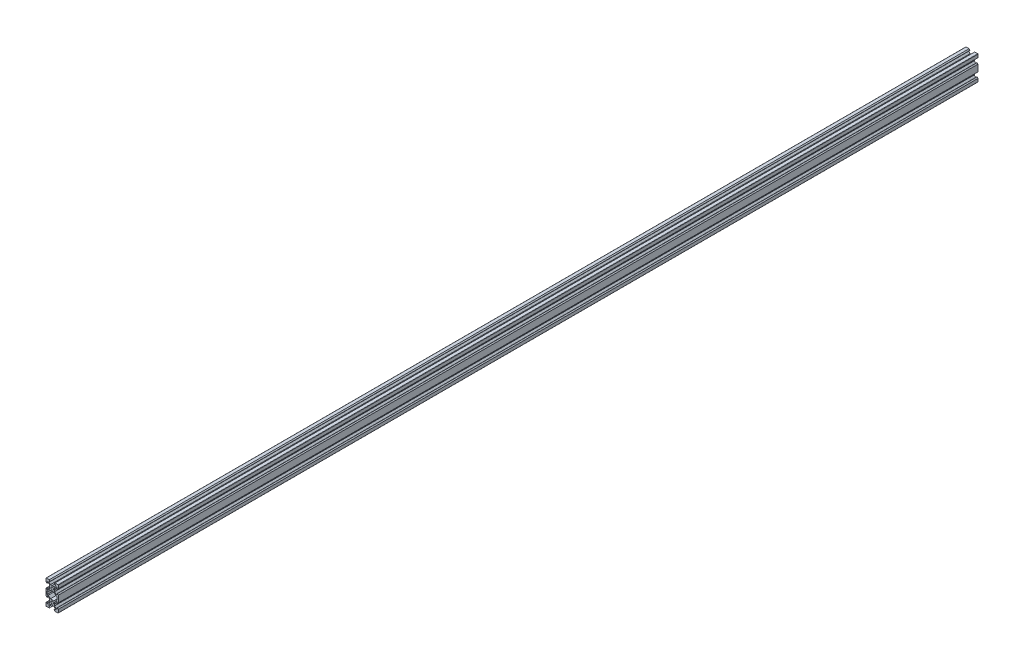
SolidWorks part; units mm, degrees
material "6061-T6 (SS)"
ref_plane "Front Plane" through (0, 0, 0) normal (0, 0, 1) x (1, 0, 0)
ref_plane "Top Plane" through (0, 0, 0) normal (0, 1, 0) x (1, 0, 0)
ref_plane "Right Plane" through (0, 0, 0) normal (1, 0, 0) x (0, 0, -1)
sketch "Sketch1" plane through (0, 0, 0) normal (0, 0, 1) x (1, 0, 0)
  line L0 (0, 0) -> (10, 0) construction
  line L1 (9.5, -20) -> (-9.5, -20)
  line L2 (10, -19.5) -> (10, 19.5)
  line L3 (9.5, 20) -> (-9.5, 20)
  line L4 (-10, -19.5) -> (-10, 19.5)
  line L5 (10, -20) -> (-10, 20) construction
  line L6 (10, 20) -> (-10, -20) construction
  circle A0 centre (0, 10) radius 2.1
  circle A1 centre (0, -10) radius 2.1
  arc A2 (-9.5, -20) -> (-10, -19.5) centre (-9.5, -19.5) cw
  arc A3 (9.5, -20) -> (10, -19.5) centre (9.5, -19.5) ccw
  arc A4 (10, 19.5) -> (9.5, 20) centre (9.5, 19.5) ccw
  arc A5 (-9.5, 20) -> (-10, 19.5) centre (-9.5, 19.5) ccw
  point P0 (0, 0)
  line B0 (0, 10) -> (0, 20) construction
  line B1 (0, 13.69) -> (-0.21, 13.9)
  line B2 (-0.21, 13.9) -> (-2.8393, 13.9)
  line B3 (-2.8393, 13.9) -> (-5.5, 16.5607)
  line B4 (-5.5, 16.5607) -> (-5.5, 18.2)
  line B5 (-5.5, 18.2) -> (-3.125, 18.2)
  line B6 (-3.125, 18.2) -> (-3.125, 18.545)
  line B7 (-3.125, 18.545) -> (-4.58, 20)
  line B8 (-4.58, 20) -> (4.58, 20)
  line B9 (0, 10) -> (-5.9132, 15.9132) construction
  line B10 (3.125, 18.545) -> (4.58, 20)
  line B11 (3.125, 18.2) -> (3.125, 18.545)
  line B12 (5.5, 18.2) -> (3.125, 18.2)
  line B13 (5.5, 16.5607) -> (5.5, 18.2)
  line B14 (2.8393, 13.9) -> (5.5, 16.5607)
  line B15 (0.21, 13.9) -> (2.8393, 13.9)
  line B16 (0, 13.69) -> (0.21, 13.9)
  line B17 (0, 10) -> (-10, 10) construction
  line B18 (-3.69, 10) -> (-3.9, 9.79)
  line B19 (-3.9, 9.79) -> (-3.9, 7.1607)
  line B20 (-3.9, 7.1607) -> (-6.5607, 4.5)
  line B21 (-6.5607, 4.5) -> (-8.2, 4.5)
  line B22 (-8.2, 4.5) -> (-8.2, 6.875)
  line B23 (-8.2, 6.875) -> (-8.545, 6.875)
  line B24 (-8.545, 6.875) -> (-10, 5.42)
  line B25 (-10, 5.42) -> (-10, 14.58)
  line B26 (0, 10) -> (-5.9132, 4.0868) construction
  line B27 (-8.545, 13.125) -> (-10, 14.58)
  line B28 (-8.2, 13.125) -> (-8.545, 13.125)
  line B29 (-8.2, 15.5) -> (-8.2, 13.125)
  line B30 (-6.5607, 15.5) -> (-8.2, 15.5)
  line B31 (-3.9, 12.8393) -> (-6.5607, 15.5)
  line B32 (-3.9, 10.21) -> (-3.9, 12.8393)
  line B33 (-3.69, 10) -> (-3.9, 10.21)
  line B34 (0, -10) -> (-10, -10) construction
  line B35 (-3.69, -10) -> (-3.9, -10.21)
  line B36 (-3.9, -10.21) -> (-3.9, -12.8393)
  line B37 (-3.9, -12.8393) -> (-6.5607, -15.5)
  line B38 (-6.5607, -15.5) -> (-8.2, -15.5)
  line B39 (-8.2, -15.5) -> (-8.2, -13.125)
  line B40 (-8.2, -13.125) -> (-8.545, -13.125)
  line B41 (-8.545, -13.125) -> (-10, -14.58)
  line B42 (-10, -14.58) -> (-10, -5.42)
  line B43 (0, -10) -> (-5.9132, -15.9132) construction
  line B44 (-8.545, -6.875) -> (-10, -5.42)
  line B45 (-8.2, -6.875) -> (-8.545, -6.875)
  line B46 (-8.2, -4.5) -> (-8.2, -6.875)
  line B47 (-6.5607, -4.5) -> (-8.2, -4.5)
  line B48 (-3.9, -7.1607) -> (-6.5607, -4.5)
  line B49 (-3.9, -9.79) -> (-3.9, -7.1607)
  line B50 (-3.69, -10) -> (-3.9, -9.79)
  line B51 (0, -10) -> (0, -20) construction
  line B52 (0, -13.69) -> (0.21, -13.9)
  line B53 (0.21, -13.9) -> (2.8393, -13.9)
  line B54 (2.8393, -13.9) -> (5.5, -16.5607)
  line B55 (5.5, -16.5607) -> (5.5, -18.2)
  line B56 (5.5, -18.2) -> (3.125, -18.2)
  line B57 (3.125, -18.2) -> (3.125, -18.545)
  line B58 (3.125, -18.545) -> (4.58, -20)
  line B59 (4.58, -20) -> (-4.58, -20)
  line B60 (0, -10) -> (5.9132, -15.9132) construction
  line B61 (-3.125, -18.545) -> (-4.58, -20)
  line B62 (-3.125, -18.2) -> (-3.125, -18.545)
  line B63 (-5.5, -18.2) -> (-3.125, -18.2)
  line B64 (-5.5, -16.5607) -> (-5.5, -18.2)
  line B65 (-2.8393, -13.9) -> (-5.5, -16.5607)
  line B66 (-0.21, -13.9) -> (-2.8393, -13.9)
  line B67 (0, -13.69) -> (-0.21, -13.9)
  line B68 (0, -10) -> (10, -10) construction
  line B69 (3.69, -10) -> (3.9, -9.79)
  line B70 (3.9, -9.79) -> (3.9, -7.1607)
  line B71 (3.9, -7.1607) -> (6.5607, -4.5)
  line B72 (6.5607, -4.5) -> (8.2, -4.5)
  line B73 (8.2, -4.5) -> (8.2, -6.875)
  line B74 (8.2, -6.875) -> (8.545, -6.875)
  line B75 (8.545, -6.875) -> (10, -5.42)
  line B76 (10, -5.42) -> (10, -14.58)
  line B77 (0, -10) -> (5.9132, -4.0868) construction
  line B78 (8.545, -13.125) -> (10, -14.58)
  line B79 (8.2, -13.125) -> (8.545, -13.125)
  line B80 (8.2, -15.5) -> (8.2, -13.125)
  line B81 (6.5607, -15.5) -> (8.2, -15.5)
  line B82 (3.9, -12.8393) -> (6.5607, -15.5)
  line B83 (3.9, -10.21) -> (3.9, -12.8393)
  line B84 (3.69, -10) -> (3.9, -10.21)
  line B85 (0, 10) -> (10, 10) construction
  line B86 (3.69, 10) -> (3.9, 10.21)
  line B87 (3.9, 10.21) -> (3.9, 12.8393)
  line B88 (3.9, 12.8393) -> (6.5607, 15.5)
  line B89 (6.5607, 15.5) -> (8.2, 15.5)
  line B90 (8.2, 15.5) -> (8.2, 13.125)
  line B91 (8.2, 13.125) -> (8.545, 13.125)
  line B92 (8.545, 13.125) -> (10, 14.58)
  line B93 (10, 14.58) -> (10, 5.42)
  line B94 (0, 10) -> (5.9132, 15.9132) construction
  line B95 (8.545, 6.875) -> (10, 5.42)
  line B96 (8.2, 6.875) -> (8.545, 6.875)
  line B97 (8.2, 4.5) -> (8.2, 6.875)
  line B98 (6.5607, 4.5) -> (8.2, 4.5)
  line B99 (3.9, 7.1607) -> (6.5607, 4.5)
  line B100 (3.9, 9.79) -> (3.9, 7.1607)
  line B101 (3.69, 10) -> (3.9, 9.79)
  line B102 (-8.2, -2.7) -> (-8.2, 2.7)
  line B103 (-8.2, 2.7) -> (-6.2393, 2.7)
  line B104 (-6.2393, 2.7) -> (-2.8393, 6.1)
  line B105 (-2.8393, 6.1) -> (2.8393, 6.1)
  line B106 (0, 6.1) -> (0, 0) construction
  line B107 (0, 0) -> (-8.2, 0) construction
  line B108 (6.2393, 2.7) -> (2.8393, 6.1)
  line B109 (8.2, 2.7) -> (6.2393, 2.7)
  line B110 (8.2, -2.7) -> (8.2, 2.7)
  line B111 (8.2, -2.7) -> (6.2393, -2.7)
  line B112 (6.2393, -2.7) -> (2.8393, -6.1)
  line B113 (-2.8393, -6.1) -> (2.8393, -6.1)
  line B114 (-6.2393, -2.7) -> (-2.8393, -6.1)
  line B115 (-8.2, -2.7) -> (-6.2393, -2.7)
  line B116 (0, 6.1) -> (0, 10) construction
  line B117 (0, 10) -> (-5.0927, 4.9073) construction
  dimension "D4" = 4.2
  dimension "D5" = 0.5
  dimension "D1" = 20
  dimension "D2" = 40
  dimension "D3" = 20
sketch_block_instance "V Slot 1-4"
sketch_block "V Slot 1" parameters "D1"=10, "D2"=11, "D3"=4.3, "D4"=1.8, "D5"=0.21, "D6"=45, "D7"=9.16, "D8"=1.5, "D9"=6.25
sketch_block_instance "V Slot 1-5"
sketch_block_instance "V Slot 1-6"
sketch_block_instance "V Slot 1-7"
sketch_block_instance "V Slot 1-8"
sketch_block_instance "V Slot 1-9"
sketch_block_instance "Center Cutout 1-1"
sketch_block "Center Cutout 1" parameters "D1"=5.4, "D2"=12.2, "D3"=8.2, "D4"=45, "D5"=10, "D6"=1.5
extrude "Boss-Extrude1" add sketch "Sketch1" along normal blind 1500 contours B101 B86 B87 B88 B89 B90 B91 B92 L2 A4 L3 B10 B11 B12 B13 B14 B15 B16 B1 B2 B3 B4 B5 B6 B7 A5 L4 B27 B28 B29 B30 B31 B32 B33 B18 B19 B20 B21 B22 B23 B24 B44 B45 B46 B47 B48 B49 B50 B35
